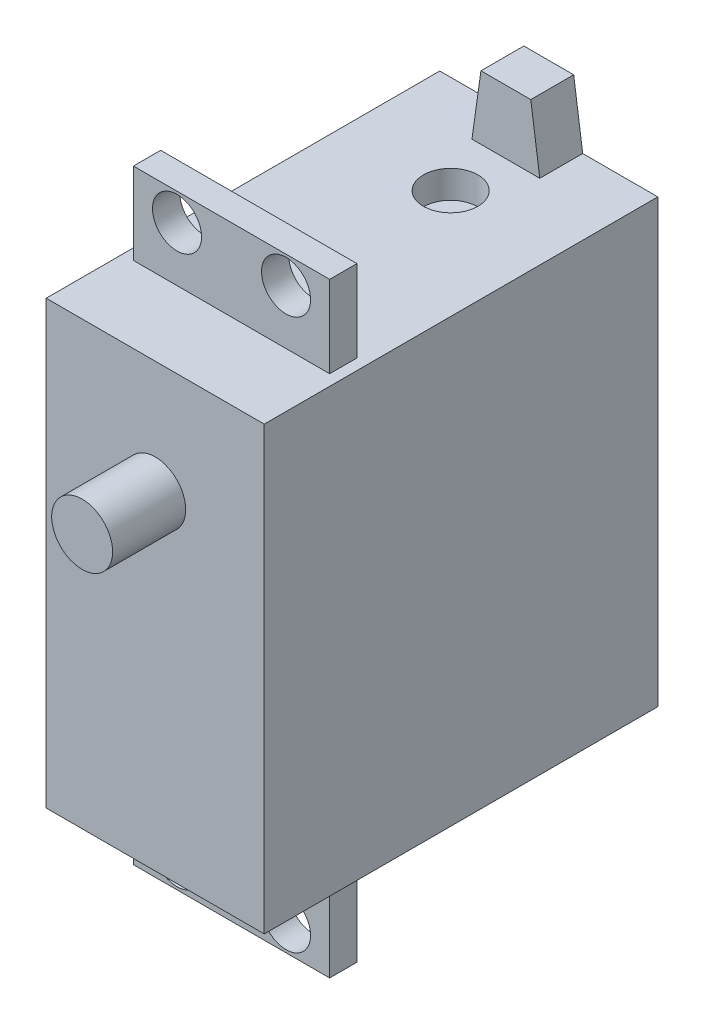
SolidWorks part; units mm, degrees
ref_plane "Front Plane" through (0, 0, 0) normal (0, 0, 1) x (1, 0, 0)
ref_plane "Top Plane" through (0, 0, 0) normal (0, 1, 0) x (1, 0, 0)
ref_plane "Right Plane" through (0, 0, 0) normal (1, 0, 0) x (0, 0, -1)
sketch "Sketch1" plane through (0, 0, 0) normal (0, 0, 1) x (1, 0, 0)
  line L1 (0, 40.5) -> (20, 40.5)
  line L2 (0, 40.5) -> (0, 0)
  line L3 (0, 0) -> (20, 0)
  line L4 (20, 40.5) -> (20, 0)
  dimension "D1" = 20
  dimension "D2" = 40.5
extrude "Boss-Extrude1" add sketch "Sketch1" along normal mid plane 19
sketch "Sketch2" plane through (0, 0, -9.5) normal (0, 0, -1) x (-1, 0, 0)
  line L0 (-20, 40.5) -> (0, 40.5) construction
  line L1 (-20, 40.5) -> (0, 40.5)
  line L2 (-20, 40.5) -> (-20, 0)
  line L3 (-20, 0) -> (0, 0)
  line L4 (0, 40.5) -> (0, 0)
  line L5 (-20, 0) -> (-20, 40.5) construction
  line L6 (0, 40.5) -> (0, 0) construction
extrude "Boss-Extrude2" add sketch "Sketch2" along normal blind 17.1
sketch "Sketch3" plane through (0, 0, 0) normal (0, 0, 1) x (1, 0, 0)
  line L0 (0, 0) -> (20, 0) construction
  line L1 (19, 0) -> (1, 0) construction
  line L2 (19, 0) -> (19, -7.5)
  line L3 (20, 40.5) -> (20, 0)
  line L4 (1, 0) -> (1, -7.5)
  line L5 (20, 40.5) -> (0, 40.5) construction
  line L6 (0, 40.5) -> (0, 0)
  line L7 (19, 48) -> (19, 40.5)
  line L8 (19, 40.5) -> (1, 40.5) construction
  line L9 (1, 48) -> (1, 40.5)
  line L10 (20, 0) -> (19, 0)
  line L11 (1, 0) -> (0, 0)
  line L12 (20, 40.5) -> (19, 40.5)
  line L13 (1, 40.5) -> (0, 40.5)
  line L14 (0, 40.5) -> (0, 0) construction
  line L15 (20, 0) -> (20, 40.5) construction
  line L19 (1, 48) -> (19, 48)
  line L20 (1, -7.5) -> (19, -7.5)
  line L24 (10, 48) -> (10, 45.5) construction
  line L25 (10, -7.5) -> (10, -5) construction
  line L28 (15, 45.5) -> (15, -5) construction
  line L29 (5, 45.5) -> (5, -5) construction
  line L30 (5, -5) -> (15, -5) construction
  line L31 (5, 45.5) -> (15, 45.5) construction
  circle A0 centre (5, -5) radius 2.25
  circle A1 centre (15, -5) radius 2.25
  circle A2 centre (5, 45.5) radius 2.25
  circle A3 centre (15, 45.5) radius 2.25
  dimension "D6" = 4.5
  dimension "D1" = 18
  dimension "D2" = 55.5
  dimension "D3" = 50.5
  dimension "D4" = 10
extrude "Boss-Extrude3" add sketch "Sketch3" along normal blind 2.5
sketch "Sketch4" plane through (0, 0, 9.5) normal (0, 0, 1) x (1, 0, 0)
  line L76 (0, 30.1) -> (20, 30.1) construction
  line L77 (0, 40.5) -> (0, 0) construction
  line L78 (20, 0) -> (20, 40.5) construction
  line L80 (20, 40.5) -> (0, 40.5) construction
  circle A0 centre (10, 30.1) radius 2.794
  dimension "D1" = 5.588
  dimension "D3" = 10.4
extrude "Boss-Extrude4" add sketch "Sketch4" along normal blind 6.7021
sketch "Sketch6" plane through (0, 0, 2.5) normal (0, 0, 1) x (1, 0, 0)
  line L0 (5, 8.61) -> (5, -18.61) construction
  line L1 (1, -7.5) -> (19, -7.5) construction
  circle A0 centre (5, -5) radius 2.25 construction
  point P2 (5, -5)
sketch "Sketch7" plane through (0, 40.5, 0) normal (0, 1, 0) x (1, 0, 0)
  line L0 (10, 17.6) -> (10, 26.6) construction
  line L1 (0, 26.6) -> (20, 26.6) construction
  circle A0 centre (10, 17.6) radius 2.5
  dimension "D2" = 5
  dimension "D1" = 9
extrude "Cut-Extrude1" cut sketch "Sketch7" against normal blind 2.54
sketch "Sketch9" plane through (0, 0, -26.6) normal (0, 0, -1) x (-1, 0, 0)
  line L0 (0, 40.5) -> (-20, 40.5) construction
  line L1 (-13.1115, 40.5) -> (-6.8885, 40.5)
  line L2 (-13.1115, 40.5) -> (-12.286, 46.342)
  line L3 (-12.286, 46.342) -> (-7.714, 46.342)
  line L4 (-6.8885, 40.5) -> (-7.714, 46.342)
  line L5 (-10, 40.5) -> (-10, 46.342) construction
  point P4 (-10, 40.5)
  dimension "D1" = 6.223
  dimension "D2" = 4.572
  dimension "D3" = 5.842
extrude "Boss-Extrude6" add sketch "Sketch9" against normal blind 3.937
